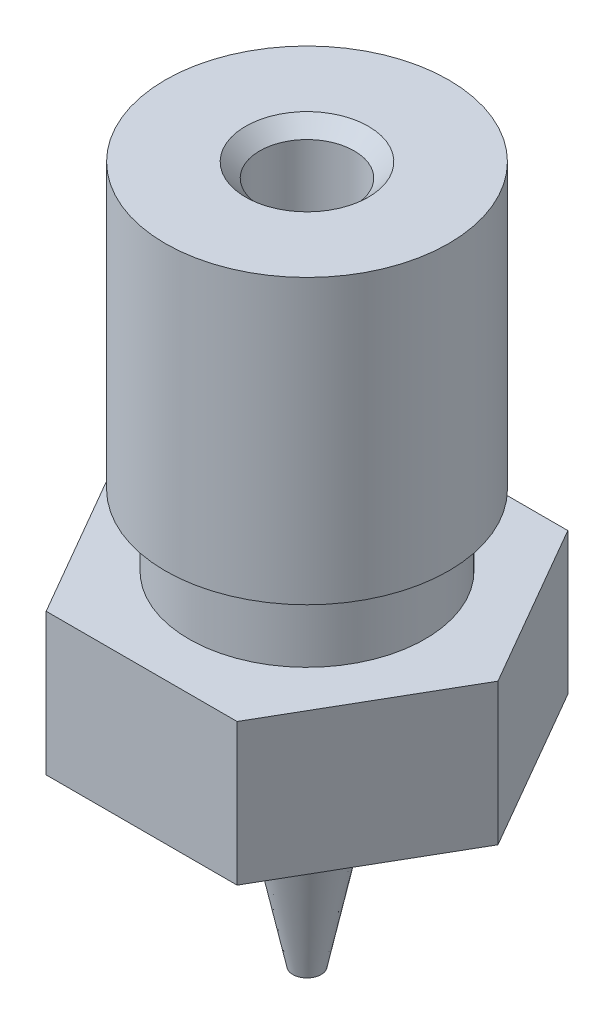
SolidWorks part; units mm, degrees
material "Brass"
ref_plane "Front Plane" through (0, 0, 0) normal (0, 0, 1) x (1, 0, 0)
ref_plane "Top Plane" through (0, 0, 0) normal (0, 1, 0) x (1, 0, 0)
ref_plane "Right Plane" through (0, 0, 0) normal (1, 0, 0) x (0, 0, -1)
sketch "Sketch1" plane through (0, 0, 0) normal (0, 0, 1) x (1, 0, 0)
  line L0 (0, 0) -> (0.5, 0)
  line L1 (0.5, 0) -> (1.9004, 2)
  line L2 (1.9004, 2) -> (3.5, 2)
  line L3 (3.5, 2) -> (3.5, 5)
  line L4 (3.5, 5) -> (2.5, 5)
  line L5 (2.5, 5) -> (2.5, 6.5)
  line L6 (2.5, 6.5) -> (3, 6.5)
  line L7 (3, 6.5) -> (3, 12.5)
  line L8 (3, 12.5) -> (0, 12.5)
  line L9 (0, 12.5) -> (0, 0)
  line L11 (0, -1.1291) -> (0, -50001.1291) construction
  dimension "D1" = 125
  dimension "D2" = 1
  dimension "D3" = 7
  dimension "D4" = 5
  dimension "D5" = 6
  dimension "D6" = 6
  dimension "D7" = 7.5
  dimension "D8" = 10.5
  dimension "D9" = 12.5
revolve "Revolve1" add sketch "Sketch1" angle 360 about L11
sketch "Sketch2" plane through (0, 0, 0) normal (0, 0, 1) x (1, 0, 0)
  line L0 (0, 0) -> (0, 12.5) construction
  line L1 (3, 12.5) -> (-3, 12.5) construction
  line L2 (0, 12.5) -> (1.3, 12.5)
  line L3 (1, 12.2) -> (1, 1.9856)
  line L4 (1, 1.9856) -> (0.2, 0.6)
  line L5 (0.2, 0.6) -> (0.2, 0)
  line L6 (-0.5, 0) -> (0.5, 0) construction
  line L7 (0.2, 0) -> (0, 0)
  line L8 (0, 0) -> (0, 12.5)
  line L9 (1, 12.2) -> (1.3, 12.5)
  dimension "D1" = 0.4
  dimension "D2" = 2
  dimension "D3" = 1.3
  dimension "D4" = 30
  dimension "D5" = 0.6
  dimension "D6" = 45
revolve "Cut-Revolve1" cut sketch "Sketch2" angle 360 about L0
sketch "Sketch3" plane through (0, 2, 0) normal (0, -1, 0) x (1, 0, 0)
  line L1 (4.0415, 0) -> (2.0207, 3.5)
  line L2 (2.0207, 3.5) -> (-2.0207, 3.5)
  line L3 (-2.0207, 3.5) -> (-4.0415, 0)
  line L4 (-4.0415, 0) -> (-2.0207, -3.5)
  line L5 (-2.0207, -3.5) -> (2.0207, -3.5)
  line L6 (2.0207, -3.5) -> (4.0415, 0)
  circle A0 centre (0, 0) radius 3.5 construction
  circle A1 centre (0, 0) radius 3.5
  circle A2 centre (0, 0) radius 3.5
  circle M3 centre (0, 0) radius 3.5
  dimension "D1" = 0
extrude "Boss-Extrude1" add sketch "Sketch3" against normal blind 3 contours L3 L4 M3 | L2 L3 M3 | L1 L2 M3 | L5 L6 M3 | L4 L5 M3 | L6 L1 M3
sketch "Sketch4" plane through (0, 0, 0) normal (0, 0, 1) x (1, 0, 0)
  line L0 (0, 2) -> (0, -2.25) construction
  line L1 (2.0207, 2) -> (-2.0207, 2) construction
  line L2 (0, -2.25) -> (0.3, -2.25)
  line L3 (0.3, -2.25) -> (0.8851, 0.55)
  line L4 (1.3, 2) -> (0, 2)
  line L5 (0.8851, 0.55) -> (1.3, 0.55)
  line L6 (1.3, 0.55) -> (1.3, 2)
  line L7 (0.5, 0) -> (1.9004, 2) construction
  line L8 (0, 2) -> (0, -2.25)
  line L9 (0.2, 0.6) -> (1, 1.9856)
  line L10 (-1, 1.9856) -> (-0.2, 0.6)
  line L12 (0.2, 0.6) -> (1.0083, 2)
  line L13 (-0.2, 0.6) -> (-0.2, 0)
  line L14 (0.2, 0) -> (0.2, 0.6)
  line L15 (0.2, 0) -> (0.2, 0.6)
  line L17 (0.2, 0) -> (0, 0)
  dimension "D1" = 0.6
  dimension "D2" = 4.25
  dimension "D3" = 2.6
  dimension "D4" = 1.45
revolve "Revolve2" add sketch "Sketch4" angle 360 about L0
